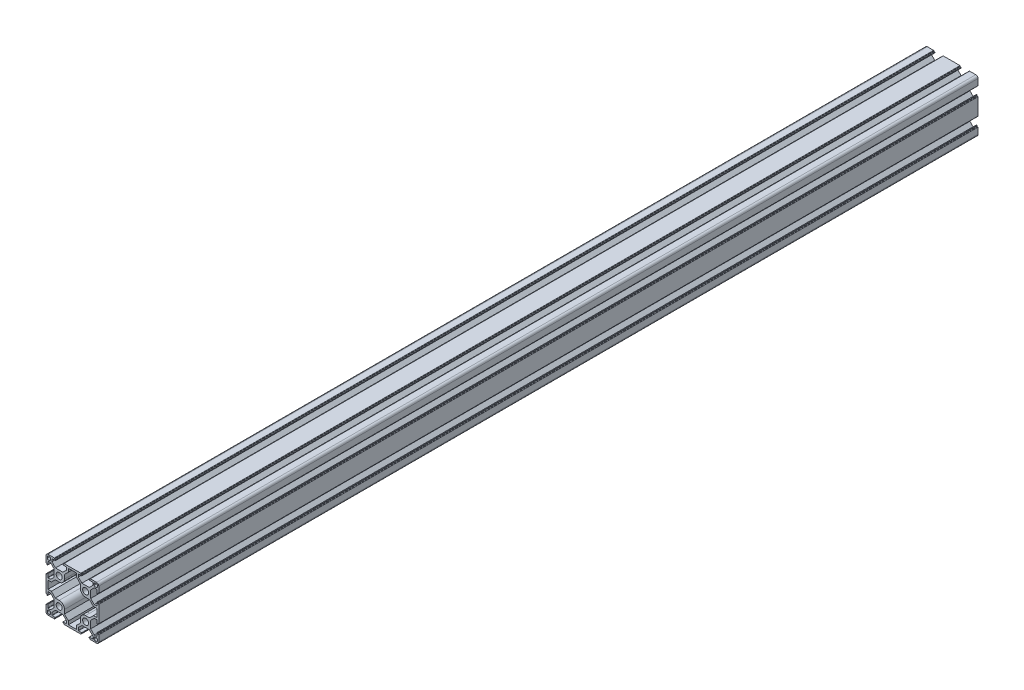
SolidWorks part; units mm, degrees
material "6063 T5"
ref_plane "Спереди" through (0, 0, 0) normal (0, 0, 1) x (1, 0, 0)
ref_plane "Сверху" through (0, 0, 0) normal (0, 1, 0) x (1, 0, 0)
ref_plane "Справа" through (0, 0, 0) normal (1, 0, 0) x (0, 0, -1)
sketch "Эскиз1" plane through (0, 0, 0) normal (0, 0, 1) x (1, 0, 0)
  line L0 (-34.4622, 45.0307) -> (-34.4622, -44.9693) construction
  line L1 (0, 30) -> (0, -30) construction
  line L2 (30, 0) -> (-30, 0) construction
  line L3 (-30, 23.25) -> (-30, 27.5)
  line L4 (-27.5, 30) -> (-23.25, 30)
  line L5 (4.5, 27.8) -> (-4.5, 27.8)
  line L6 (-27.35, 28.55) -> (-25.95, 28.55)
  line L7 (-28.55, 27.35) -> (-28.55, 25.95)
  line L8 (-27.35, 24.75) -> (-25.95, 24.75)
  line L9 (-24.75, 27.35) -> (-24.75, 25.95)
  line L10 (-4.5, 27.8) -> (-4.5, 23.9887)
  line L11 (-4.5, 23.9887) -> (-9, 19.4887)
  line L12 (-9, 19.4887) -> (-9, 15)
  line L13 (-15, 9) -> (-19.4887, 9)
  line L14 (-19.4887, 9) -> (-23.9387, 4.55)
  line L15 (-23.9387, 4.55) -> (-27.8, 4.55)
  line L16 (-27.8, 4.55) -> (-27.8, -4.55)
  line L21 (-6.75, 30) -> (6.75, 30)
  line L22 (-30, 6.75) -> (-30, -6.75)
  line L23 (30, 6.75) -> (30, -6.75)
  line L24 (27.5, 30) -> (23.25, 30)
  line L25 (30, 23.25) -> (30, 27.5)
  line L29 (27.8, 4.55) -> (27.8, -4.55)
  line L30 (23.9387, 4.55) -> (27.8, 4.55)
  line L31 (19.4887, 9) -> (23.9387, 4.55)
  line L32 (15, 9) -> (19.4887, 9)
  line L33 (9, 19.4887) -> (9, 15)
  line L34 (4.5, 23.9887) -> (9, 19.4887)
  line L35 (4.5, 27.8) -> (4.5, 23.9887)
  line L36 (27.35, 28.55) -> (25.95, 28.55)
  line L37 (28.55, 27.35) -> (28.55, 25.95)
  line L38 (27.35, 24.75) -> (25.95, 24.75)
  line L39 (24.75, 27.35) -> (24.75, 25.95)
  line L40 (24.75, -27.35) -> (24.75, -25.95)
  line L41 (27.35, -24.75) -> (25.95, -24.75)
  line L42 (28.55, -27.35) -> (28.55, -25.95)
  line L43 (27.35, -28.55) -> (25.95, -28.55)
  line L44 (4.5, -27.8) -> (4.5, -23.9887)
  line L45 (4.5, -23.9887) -> (9, -19.4887)
  line L46 (9, -19.4887) -> (9, -15)
  line L47 (15, -9) -> (19.4887, -9)
  line L48 (19.4887, -9) -> (23.9387, -4.55)
  line L49 (23.9387, -4.55) -> (27.8, -4.55)
  line L51 (30, -23.25) -> (30, -27.5)
  line L52 (27.5, -30) -> (23.25, -30)
  line L55 (-6.75, -30) -> (6.75, -30)
  line L57 (-23.9387, -4.55) -> (-27.8, -4.55)
  line L58 (-19.4887, -9) -> (-23.9387, -4.55)
  line L59 (-15, -9) -> (-19.4887, -9)
  line L60 (-9, -19.4887) -> (-9, -15)
  line L61 (-4.5, -23.9887) -> (-9, -19.4887)
  line L62 (-4.5, -27.8) -> (-4.5, -23.9887)
  line L63 (-24.75, -27.35) -> (-24.75, -25.95)
  line L64 (-27.35, -24.75) -> (-25.95, -24.75)
  line L65 (-28.55, -27.35) -> (-28.55, -25.95)
  line L66 (-27.35, -28.55) -> (-25.95, -28.55)
  line L67 (4.5, -27.8) -> (-4.5, -27.8)
  line L68 (-27.5, -30) -> (-23.25, -30)
  line L69 (-30, -23.25) -> (-30, -27.5)
  line L70 (-30.0267, 37.312) -> (29.9733, 37.312) construction
  arc A0 (-30, 27.5) -> (-27.5, 30) centre (-27.5, 27.5) cw
  arc A1 (-28.55, 25.95) -> (-27.35, 24.75) centre (-27.35, 25.95) ccw
  arc A2 (-25.95, 24.75) -> (-24.75, 25.95) centre (-25.95, 25.95) ccw
  arc A3 (-25.95, 28.55) -> (-24.75, 27.35) centre (-25.95, 27.35) cw
  arc A4 (-27.35, 28.55) -> (-28.55, 27.35) centre (-27.35, 27.35) ccw
  circle A5 centre (-15, 15) radius 3.4
  arc A6 (-9, 15) -> (-15, 9) centre (-15, 15) cw
  arc A9 (30, 27.5) -> (27.5, 30) centre (27.5, 27.5) ccw
  arc A11 (9, 15) -> (15, 9) centre (15, 15) ccw
  circle A12 centre (15, 15) radius 3.4
  arc A14 (25.95, 28.55) -> (24.75, 27.35) centre (25.95, 27.35) ccw
  arc A15 (27.35, 28.55) -> (28.55, 27.35) centre (27.35, 27.35) cw
  arc A16 (28.55, 25.95) -> (27.35, 24.75) centre (27.35, 25.95) cw
  arc A17 (25.95, 24.75) -> (24.75, 25.95) centre (25.95, 25.95) cw
  arc A18 (25.95, -24.75) -> (24.75, -25.95) centre (25.95, -25.95) ccw
  arc A19 (28.55, -25.95) -> (27.35, -24.75) centre (27.35, -25.95) ccw
  arc A20 (27.35, -28.55) -> (28.55, -27.35) centre (27.35, -27.35) ccw
  arc A21 (25.95, -28.55) -> (24.75, -27.35) centre (25.95, -27.35) cw
  circle A22 centre (15, -15) radius 3.4
  arc A23 (9, -15) -> (15, -9) centre (15, -15) cw
  arc A24 (30, -27.5) -> (27.5, -30) centre (27.5, -27.5) cw
  arc A25 (-9, -15) -> (-15, -9) centre (-15, -15) ccw
  circle A26 centre (-15, -15) radius 3.4
  arc A27 (-27.35, -28.55) -> (-28.55, -27.35) centre (-27.35, -27.35) cw
  arc A28 (-25.95, -28.55) -> (-24.75, -27.35) centre (-25.95, -27.35) ccw
  arc A29 (-25.95, -24.75) -> (-24.75, -25.95) centre (-25.95, -25.95) cw
  arc A30 (-28.55, -25.95) -> (-27.35, -24.75) centre (-27.35, -25.95) cw
  arc A31 (-30, -27.5) -> (-27.5, -30) centre (-27.5, -27.5) ccw
  point P22 (-24.75, 28.55)
  point P25 (-28.55, 28.55)
  point P63 (0, 1.1)
  point P72 (0, 27.8)
  point P114 (0, -27.8)
  point P115 (0, -1.1)
  point P122 (27.8, 0)
  point P125 (30, 0)
  point P129 (-27.8, 0)
  line B0 (-30, 23.25) -> (-30, 20.5)
  line B1 (-29.7, 20.2) -> (-29.3, 20.2)
  line B2 (-29, 19.9) -> (-29, 19.4)
  line B3 (-28.7, 19.1) -> (-28.3, 19.1)
  line B4 (-28, 19.4) -> (-28, 22.95)
  line B5 (-27.7, 23.25) -> (-24.85, 23.25)
  line B6 (-24.85, 23.25) -> (-20.8, 19.2)
  line B7 (-20.8, 15) -> (-30, 15) construction
  line B8 (-20.8, 10.8) -> (-20.8, 19.2)
  line B9 (-24.85, 6.75) -> (-20.8, 10.8)
  line B10 (-27.7, 6.75) -> (-24.85, 6.75)
  line B11 (-28, 10.6) -> (-28, 7.05)
  line B12 (-28.7, 10.9) -> (-28.3, 10.9)
  line B13 (-29, 10.1) -> (-29, 10.6)
  line B14 (-29.7, 9.8) -> (-29.3, 9.8)
  line B15 (-30, 6.75) -> (-30, 9.5)
  arc B16 (-28, 22.95) -> (-27.7, 23.25) centre (-27.7, 22.95) cw
  arc B17 (-28.3, 19.1) -> (-28, 19.4) centre (-28.3, 19.4) ccw
  arc B18 (-29, 19.4) -> (-28.7, 19.1) centre (-28.7, 19.4) ccw
  arc B19 (-29.3, 20.2) -> (-29, 19.9) centre (-29.3, 19.9) cw
  arc B20 (-30, 20.5) -> (-29.7, 20.2) centre (-29.7, 20.5) ccw
  arc B21 (-30, 9.5) -> (-29.7, 9.8) centre (-29.7, 9.5) cw
  arc B22 (-29.3, 9.8) -> (-29, 10.1) centre (-29.3, 10.1) ccw
  arc B23 (-29, 10.6) -> (-28.7, 10.9) centre (-28.7, 10.6) cw
  arc B24 (-28.3, 10.9) -> (-28, 10.6) centre (-28.3, 10.6) cw
  arc B25 (-28, 7.05) -> (-27.7, 6.75) centre (-27.7, 7.05) ccw
  line B26 (-6.75, 30) -> (-9.5, 30)
  line B27 (-9.8, 29.7) -> (-9.8, 29.3)
  line B28 (-10.1, 29) -> (-10.6, 29)
  line B29 (-10.9, 28.7) -> (-10.9, 28.3)
  line B30 (-10.6, 28) -> (-7.05, 28)
  line B31 (-6.75, 27.7) -> (-6.75, 24.85)
  line B32 (-6.75, 24.85) -> (-10.8, 20.8)
  line B33 (-15, 20.8) -> (-15, 30) construction
  line B34 (-19.2, 20.8) -> (-10.8, 20.8)
  line B35 (-23.25, 24.85) -> (-19.2, 20.8)
  line B36 (-23.25, 27.7) -> (-23.25, 24.85)
  line B37 (-19.4, 28) -> (-22.95, 28)
  line B38 (-19.1, 28.7) -> (-19.1, 28.3)
  line B39 (-19.9, 29) -> (-19.4, 29)
  line B40 (-20.2, 29.7) -> (-20.2, 29.3)
  line B41 (-23.25, 30) -> (-20.5, 30)
  arc B42 (-7.05, 28) -> (-6.75, 27.7) centre (-7.05, 27.7) cw
  arc B43 (-10.9, 28.3) -> (-10.6, 28) centre (-10.6, 28.3) ccw
  arc B44 (-10.6, 29) -> (-10.9, 28.7) centre (-10.6, 28.7) ccw
  arc B45 (-9.8, 29.3) -> (-10.1, 29) centre (-10.1, 29.3) cw
  arc B46 (-9.5, 30) -> (-9.8, 29.7) centre (-9.5, 29.7) ccw
  arc B47 (-20.5, 30) -> (-20.2, 29.7) centre (-20.5, 29.7) cw
  arc B48 (-20.2, 29.3) -> (-19.9, 29) centre (-19.9, 29.3) ccw
  arc B49 (-19.4, 29) -> (-19.1, 28.7) centre (-19.4, 28.7) cw
  arc B50 (-19.1, 28.3) -> (-19.4, 28) centre (-19.4, 28.3) cw
  arc B51 (-22.95, 28) -> (-23.25, 27.7) centre (-22.95, 27.7) ccw
  line B52 (6.75, 30) -> (9.5, 30)
  line B53 (9.8, 29.7) -> (9.8, 29.3)
  line B54 (10.1, 29) -> (10.6, 29)
  line B55 (10.9, 28.7) -> (10.9, 28.3)
  line B56 (10.6, 28) -> (7.05, 28)
  line B57 (6.75, 27.7) -> (6.75, 24.85)
  line B58 (6.75, 24.85) -> (10.8, 20.8)
  line B59 (15, 20.8) -> (15, 30) construction
  line B60 (19.2, 20.8) -> (10.8, 20.8)
  line B61 (23.25, 24.85) -> (19.2, 20.8)
  line B62 (23.25, 27.7) -> (23.25, 24.85)
  line B63 (19.4, 28) -> (22.95, 28)
  line B64 (19.1, 28.7) -> (19.1, 28.3)
  line B65 (19.9, 29) -> (19.4, 29)
  line B66 (20.2, 29.7) -> (20.2, 29.3)
  line B67 (23.25, 30) -> (20.5, 30)
  arc B68 (7.05, 28) -> (6.75, 27.7) centre (7.05, 27.7) ccw
  arc B69 (10.9, 28.3) -> (10.6, 28) centre (10.6, 28.3) cw
  arc B70 (10.6, 29) -> (10.9, 28.7) centre (10.6, 28.7) cw
  arc B71 (9.8, 29.3) -> (10.1, 29) centre (10.1, 29.3) ccw
  arc B72 (9.5, 30) -> (9.8, 29.7) centre (9.5, 29.7) cw
  arc B73 (20.5, 30) -> (20.2, 29.7) centre (20.5, 29.7) ccw
  arc B74 (20.2, 29.3) -> (19.9, 29) centre (19.9, 29.3) cw
  arc B75 (19.4, 29) -> (19.1, 28.7) centre (19.4, 28.7) ccw
  arc B76 (19.1, 28.3) -> (19.4, 28) centre (19.4, 28.3) ccw
  arc B77 (22.95, 28) -> (23.25, 27.7) centre (22.95, 27.7) cw
  line B78 (30, 23.25) -> (30, 20.5)
  line B79 (29.7, 20.2) -> (29.3, 20.2)
  line B80 (29, 19.9) -> (29, 19.4)
  line B81 (28.7, 19.1) -> (28.3, 19.1)
  line B82 (28, 19.4) -> (28, 22.95)
  line B83 (27.7, 23.25) -> (24.85, 23.25)
  line B84 (24.85, 23.25) -> (20.8, 19.2)
  line B85 (20.8, 15) -> (30, 15) construction
  line B86 (20.8, 10.8) -> (20.8, 19.2)
  line B87 (24.85, 6.75) -> (20.8, 10.8)
  line B88 (27.7, 6.75) -> (24.85, 6.75)
  line B89 (28, 10.6) -> (28, 7.05)
  line B90 (28.7, 10.9) -> (28.3, 10.9)
  line B91 (29, 10.1) -> (29, 10.6)
  line B92 (29.7, 9.8) -> (29.3, 9.8)
  line B93 (30, 6.75) -> (30, 9.5)
  arc B94 (28, 22.95) -> (27.7, 23.25) centre (27.7, 22.95) ccw
  arc B95 (28.3, 19.1) -> (28, 19.4) centre (28.3, 19.4) cw
  arc B96 (29, 19.4) -> (28.7, 19.1) centre (28.7, 19.4) cw
  arc B97 (29.3, 20.2) -> (29, 19.9) centre (29.3, 19.9) ccw
  arc B98 (30, 20.5) -> (29.7, 20.2) centre (29.7, 20.5) cw
  arc B99 (30, 9.5) -> (29.7, 9.8) centre (29.7, 9.5) ccw
  arc B100 (29.3, 9.8) -> (29, 10.1) centre (29.3, 10.1) cw
  arc B101 (29, 10.6) -> (28.7, 10.9) centre (28.7, 10.6) ccw
  arc B102 (28.3, 10.9) -> (28, 10.6) centre (28.3, 10.6) ccw
  arc B103 (28, 7.05) -> (27.7, 6.75) centre (27.7, 7.05) cw
  line B104 (6.75, -30) -> (9.5, -30)
  line B105 (9.8, -29.7) -> (9.8, -29.3)
  line B106 (10.1, -29) -> (10.6, -29)
  line B107 (10.9, -28.7) -> (10.9, -28.3)
  line B108 (10.6, -28) -> (7.05, -28)
  line B109 (6.75, -27.7) -> (6.75, -24.85)
  line B110 (6.75, -24.85) -> (10.8, -20.8)
  line B111 (15, -20.8) -> (15, -30) construction
  line B112 (19.2, -20.8) -> (10.8, -20.8)
  line B113 (23.25, -24.85) -> (19.2, -20.8)
  line B114 (23.25, -27.7) -> (23.25, -24.85)
  line B115 (19.4, -28) -> (22.95, -28)
  line B116 (19.1, -28.7) -> (19.1, -28.3)
  line B117 (19.9, -29) -> (19.4, -29)
  line B118 (20.2, -29.7) -> (20.2, -29.3)
  line B119 (23.25, -30) -> (20.5, -30)
  arc B120 (7.05, -28) -> (6.75, -27.7) centre (7.05, -27.7) cw
  arc B121 (10.9, -28.3) -> (10.6, -28) centre (10.6, -28.3) ccw
  arc B122 (10.6, -29) -> (10.9, -28.7) centre (10.6, -28.7) ccw
  arc B123 (9.8, -29.3) -> (10.1, -29) centre (10.1, -29.3) cw
  arc B124 (9.5, -30) -> (9.8, -29.7) centre (9.5, -29.7) ccw
  arc B125 (20.5, -30) -> (20.2, -29.7) centre (20.5, -29.7) cw
  arc B126 (20.2, -29.3) -> (19.9, -29) centre (19.9, -29.3) ccw
  arc B127 (19.4, -29) -> (19.1, -28.7) centre (19.4, -28.7) cw
  arc B128 (19.1, -28.3) -> (19.4, -28) centre (19.4, -28.3) cw
  arc B129 (22.95, -28) -> (23.25, -27.7) centre (22.95, -27.7) ccw
  line B130 (-6.75, -30) -> (-9.5, -30)
  line B131 (-9.8, -29.7) -> (-9.8, -29.3)
  line B132 (-10.1, -29) -> (-10.6, -29)
  line B133 (-10.9, -28.7) -> (-10.9, -28.3)
  line B134 (-10.6, -28) -> (-7.05, -28)
  line B135 (-6.75, -27.7) -> (-6.75, -24.85)
  line B136 (-6.75, -24.85) -> (-10.8, -20.8)
  line B137 (-15, -20.8) -> (-15, -30) construction
  line B138 (-19.2, -20.8) -> (-10.8, -20.8)
  line B139 (-23.25, -24.85) -> (-19.2, -20.8)
  line B140 (-23.25, -27.7) -> (-23.25, -24.85)
  line B141 (-19.4, -28) -> (-22.95, -28)
  line B142 (-19.1, -28.7) -> (-19.1, -28.3)
  line B143 (-19.9, -29) -> (-19.4, -29)
  line B144 (-20.2, -29.7) -> (-20.2, -29.3)
  line B145 (-23.25, -30) -> (-20.5, -30)
  arc B146 (-7.05, -28) -> (-6.75, -27.7) centre (-7.05, -27.7) ccw
  arc B147 (-10.9, -28.3) -> (-10.6, -28) centre (-10.6, -28.3) cw
  arc B148 (-10.6, -29) -> (-10.9, -28.7) centre (-10.6, -28.7) cw
  arc B149 (-9.8, -29.3) -> (-10.1, -29) centre (-10.1, -29.3) ccw
  arc B150 (-9.5, -30) -> (-9.8, -29.7) centre (-9.5, -29.7) cw
  arc B151 (-20.5, -30) -> (-20.2, -29.7) centre (-20.5, -29.7) ccw
  arc B152 (-20.2, -29.3) -> (-19.9, -29) centre (-19.9, -29.3) cw
  arc B153 (-19.4, -29) -> (-19.1, -28.7) centre (-19.4, -28.7) ccw
  arc B154 (-19.1, -28.3) -> (-19.4, -28) centre (-19.4, -28.3) ccw
  arc B155 (-22.95, -28) -> (-23.25, -27.7) centre (-22.95, -27.7) cw
  line B156 (30, -23.25) -> (30, -20.5)
  line B157 (29.7, -20.2) -> (29.3, -20.2)
  line B158 (29, -19.9) -> (29, -19.4)
  line B159 (28.7, -19.1) -> (28.3, -19.1)
  line B160 (28, -19.4) -> (28, -22.95)
  line B161 (27.7, -23.25) -> (24.85, -23.25)
  line B162 (24.85, -23.25) -> (20.8, -19.2)
  line B163 (20.8, -15) -> (30, -15) construction
  line B164 (20.8, -10.8) -> (20.8, -19.2)
  line B165 (24.85, -6.75) -> (20.8, -10.8)
  line B166 (27.7, -6.75) -> (24.85, -6.75)
  line B167 (28, -10.6) -> (28, -7.05)
  line B168 (28.7, -10.9) -> (28.3, -10.9)
  line B169 (29, -10.1) -> (29, -10.6)
  line B170 (29.7, -9.8) -> (29.3, -9.8)
  line B171 (30, -6.75) -> (30, -9.5)
  arc B172 (28, -22.95) -> (27.7, -23.25) centre (27.7, -22.95) cw
  arc B173 (28.3, -19.1) -> (28, -19.4) centre (28.3, -19.4) ccw
  arc B174 (29, -19.4) -> (28.7, -19.1) centre (28.7, -19.4) ccw
  arc B175 (29.3, -20.2) -> (29, -19.9) centre (29.3, -19.9) cw
  arc B176 (30, -20.5) -> (29.7, -20.2) centre (29.7, -20.5) ccw
  arc B177 (30, -9.5) -> (29.7, -9.8) centre (29.7, -9.5) cw
  arc B178 (29.3, -9.8) -> (29, -10.1) centre (29.3, -10.1) ccw
  arc B179 (29, -10.6) -> (28.7, -10.9) centre (28.7, -10.6) cw
  arc B180 (28.3, -10.9) -> (28, -10.6) centre (28.3, -10.6) cw
  arc B181 (28, -7.05) -> (27.7, -6.75) centre (27.7, -7.05) ccw
  line B182 (-30, -23.25) -> (-30, -20.5)
  line B183 (-29.7, -20.2) -> (-29.3, -20.2)
  line B184 (-29, -19.9) -> (-29, -19.4)
  line B185 (-28.7, -19.1) -> (-28.3, -19.1)
  line B186 (-28, -19.4) -> (-28, -22.95)
  line B187 (-27.7, -23.25) -> (-24.85, -23.25)
  line B188 (-24.85, -23.25) -> (-20.8, -19.2)
  line B189 (-20.8, -15) -> (-30, -15) construction
  line B190 (-20.8, -10.8) -> (-20.8, -19.2)
  line B191 (-24.85, -6.75) -> (-20.8, -10.8)
  line B192 (-27.7, -6.75) -> (-24.85, -6.75)
  line B193 (-28, -10.6) -> (-28, -7.05)
  line B194 (-28.7, -10.9) -> (-28.3, -10.9)
  line B195 (-29, -10.1) -> (-29, -10.6)
  line B196 (-29.7, -9.8) -> (-29.3, -9.8)
  line B197 (-30, -6.75) -> (-30, -9.5)
  arc B198 (-28, -22.95) -> (-27.7, -23.25) centre (-27.7, -22.95) ccw
  arc B199 (-28.3, -19.1) -> (-28, -19.4) centre (-28.3, -19.4) cw
  arc B200 (-29, -19.4) -> (-28.7, -19.1) centre (-28.7, -19.4) cw
  arc B201 (-29.3, -20.2) -> (-29, -19.9) centre (-29.3, -19.9) ccw
  arc B202 (-30, -20.5) -> (-29.7, -20.2) centre (-29.7, -20.5) cw
  arc B203 (-30, -9.5) -> (-29.7, -9.8) centre (-29.7, -9.5) ccw
  arc B204 (-29.3, -9.8) -> (-29, -10.1) centre (-29.3, -10.1) cw
  arc B205 (-29, -10.6) -> (-28.7, -10.9) centre (-28.7, -10.6) ccw
  arc B206 (-28.3, -10.9) -> (-28, -10.6) centre (-28.3, -10.6) ccw
  arc B207 (-28, -7.05) -> (-27.7, -6.75) centre (-27.7, -7.05) cw
  dimension "D6" = 2.5
  dimension "D10" = 1.2
  dimension "D11" = 6.8
  dimension "D17" = 6
  dimension "D1" = 90
  dimension "D2" = 60
  dimension "D3" = 60
  dimension "D4" = 15
  dimension "D5" = 15
  dimension "D7" = 1.5
  dimension "D8" = 1.5
  dimension "D9" = 3.8
  dimension "D12" = 2.2
  dimension "D13" = 4.5
  dimension "D14" = 2.2
  dimension "D15" = 2.2
  dimension "D16" = 2.2
  dimension "D18" = 2.2
  dimension "D19" = 60
sketch_block_instance "8B(16,5P_low)-3"
sketch_block "8B(16,5P_low)" parameters "D6"=0.3, "D1"=16.5, "D2"=8.4, "D3"=9.2, "D4"=45, "D5"=10.4, "D7"=2, "D8"=1, "D9"=8.2, "D10"=8.4
sketch_block_instance "8B(16,5P_low)-4"
sketch_block_instance "8B(16,5P_low)-5"
sketch_block_instance "8B(16,5P_low)-6"
sketch_block_instance "8B(16,5P_low)-24"
sketch_block_instance "8B(16,5P_low)-25"
sketch_block_instance "8B(16,5P_low)-26"
sketch_block_instance "8B(16,5P_low)-27"
extrude "Бобышка-Вытянуть1" add sketch "Эскиз1" along normal blind 1000 contours B193 B207 B192 B191 B190 B188 B187 B198 B186 B199 B185 B200 B184 B201 B183 B202 B182 L69 A31 L68 B145 B151 B144 B152 B143 B153 B142 B154 B141 B155 B140 B139 B138 B136 B135 B146 B134 B147 B133 B148 B132 B149 B131 B150 B130 L55 B104 B124 B105 B123 B106
